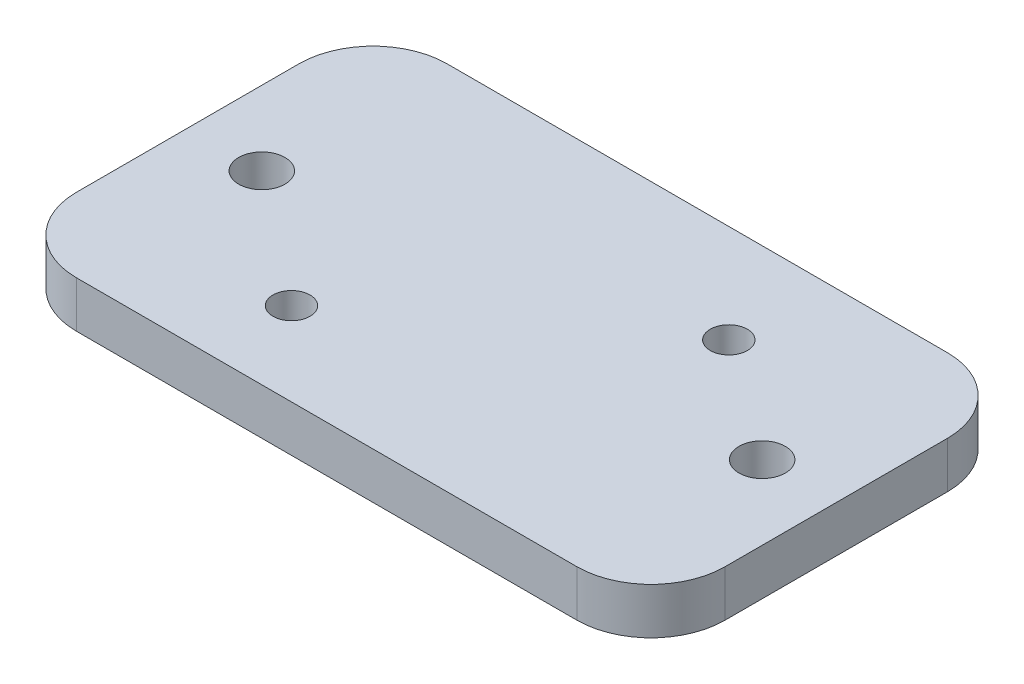
SolidWorks part; units mm, degrees
ref_plane "Front" through (0, 0, 0) normal (0, 0, 1) x (1, 0, 0)
ref_plane "Top" through (0, 0, 0) normal (0, 1, 0) x (1, 0, 0)
ref_plane "Right" through (0, 0, 0) normal (1, 0, 0) x (0, 0, -1)
sketch "Sketch1" plane through (0, 0, 0) normal (0, 1, 0) x (1, 0, 0)
  line L1 (5.08, 0) -> (39.37, 0)
  line L2 (0, 5.08) -> (0, 20.32)
  line L3 (5.08, 25.4) -> (39.37, 25.4)
  line L4 (44.45, 5.08) -> (44.45, 20.32)
  line L5 (0, 0) -> (44.45, 25.4) construction
  line L6 (0, 25.4) -> (44.45, 0) construction
  arc A0 (5.08, 0) -> (0, 5.08) centre (5.08, 5.08) cw
  arc A1 (39.37, 0) -> (44.45, 5.08) centre (39.37, 5.08) ccw
  arc A2 (39.37, 25.4) -> (44.45, 20.32) centre (39.37, 20.32) cw
  arc A3 (0, 20.32) -> (5.08, 25.4) centre (5.08, 20.32) cw
  point P4 (22.225, 12.7)
  dimension "D3" = 5.08
  dimension "D1" = 25.4
  dimension "D2" = 44.45
extrude "Boss-Extrude1" add sketch "Sketch1" along normal blind 3.175
sketch "Sketch2" plane through (0, 0, 0) normal (0, -1, 0) x (1, 0, 0)
  line L0 (22.225, -25.4) -> (22.225, 0) construction
  line L1 (39.37, -25.4) -> (5.08, -25.4) construction
  line L2 (5.08, 0) -> (39.37, 0) construction
  line L3 (5.08, -12.7) -> (0, -12.7) construction
  line L4 (0, -20.32) -> (0, -5.08) construction
  circle A0 centre (5.08, -12.7) radius 1.5875
  circle A1 centre (39.37, -12.7) radius 1.5875
  dimension "D1" = 3.175
  dimension "D2" = 5.08
extrude "Cut-Extrude1" cut sketch "Sketch2" against normal up to next
sketch "Sketch3" plane through (0, 0, 0) normal (0, -1, 0) x (1, 0, 0)
  circle A0 centre (14.097, -5.715) radius 1.778 construction
  circle A1 centre (14.097, -5.715) radius 1.778 construction
  circle A2 centre (31.115, -18.669) radius 1.778 construction
  circle A3 centre (31.115, -18.669) radius 1.778 construction
  circle A4 centre (14.097, -5.715) radius 1.27
  circle A5 centre (31.115, -18.669) radius 1.27
  dimension "D1" = 2.54
  dimension "D2" = 2.54
extrude "Cut-Extrude2" cut sketch "Sketch3" against normal up to next
sketch "Sketch4" plane through (0, 0, 0) normal (0, -1, 0) x (1, 0, 0)
  line L3 (13.3435, -19.8941) -> (29.0312, -19.8941)
  line L5 (13.3435, -22.6506) -> (29.0312, -22.6506)
  arc A2 (13.3435, -19.8941) -> (13.3435, -22.6506) centre (13.3435, -21.2723) ccw
  arc A3 (29.0312, -22.6506) -> (29.0312, -19.8941) centre (29.0312, -21.2723) ccw
extrude "Cut-Extrude3" cut sketch "Sketch4" against normal blind 1.5875
